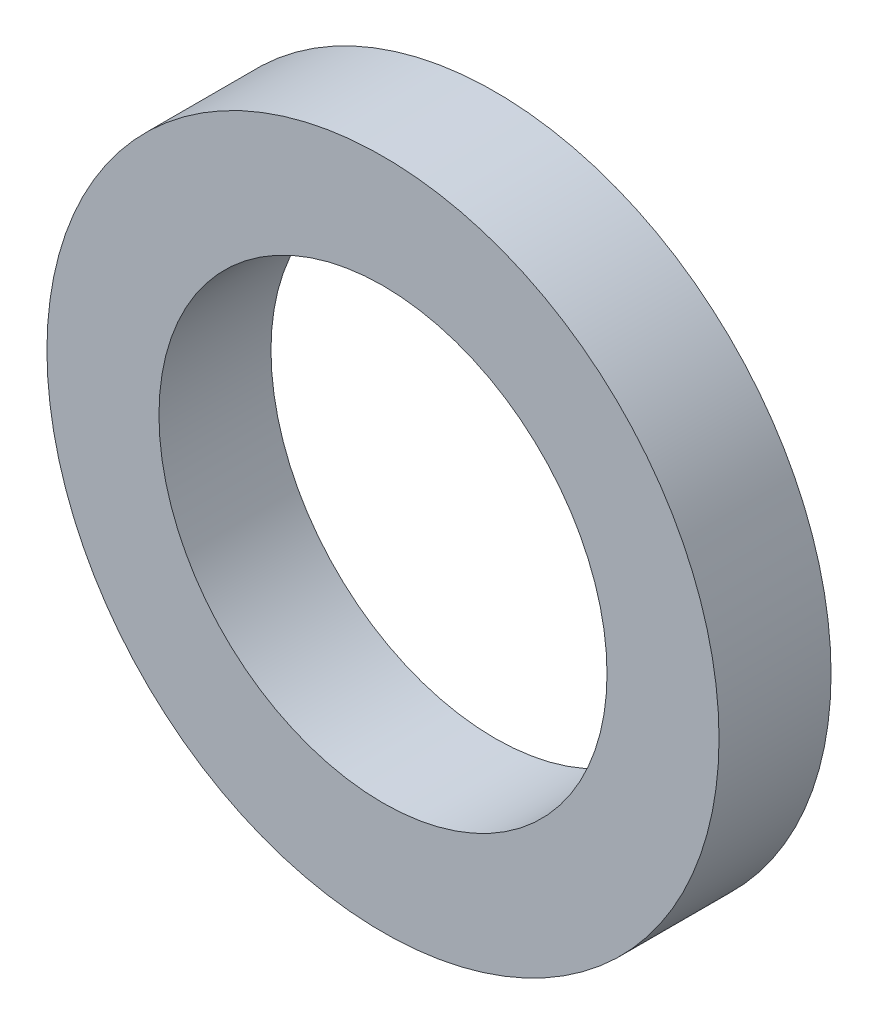
SolidWorks part; units mm, degrees
ref_plane "Front Plane" through (0, 0, 0) normal (0, 0, 1) x (1, 0, 0)
ref_plane "Top Plane" through (0, 0, 0) normal (0, 1, 0) x (1, 0, 0)
ref_plane "Right Plane" through (0, 0, 0) normal (1, 0, 0) x (0, 0, -1)
sketch "Sketch1" plane through (0, 0, 0) normal (0, 0, 1) x (1, 0, 0)
  circle A0 centre (0, 0) radius 10
  circle A1 centre (0, 0) radius 15
  dimension "D1" = 20
  dimension "D2" = 30
extrude "Boss-Extrude2" add sketch "Sketch1" along normal blind 5
